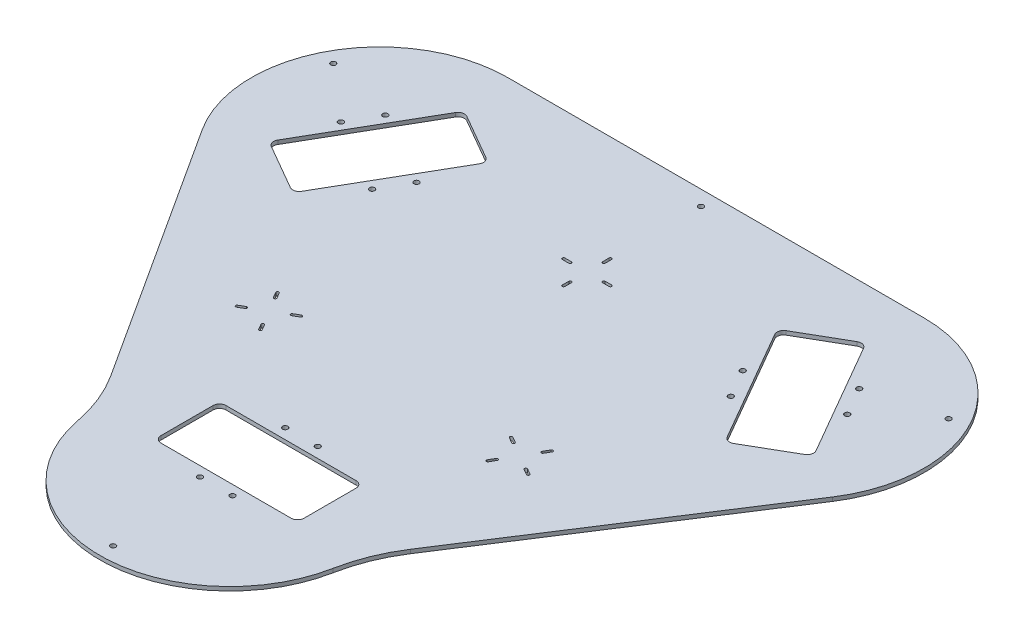
SolidWorks part; units mm, degrees
ref_plane "Front Plane" through (0, 0, 0) normal (0, 0, 1) x (1, 0, 0)
ref_plane "Top Plane" through (0, 0, 0) normal (0, 1, 0) x (1, 0, 0)
ref_plane "Right Plane" through (0, 0, 0) normal (1, 0, 0) x (0, 0, -1)
sketch "Sketch2" plane through (0, 0, 0) normal (0, 1, 0) x (1, 0, 0)
  line L0 (0, 0) -> (0, -160) construction
  line L1 (-113.959, -159.7076) -> (-242.8524, 39.5739)
  line L2 (116.6028, -159.7076) -> (244.0604, 37.3539)
  line L3 (-160.0904, 191.6683) -> (160.0904, 191.6683)
  line L8 (0, 0) -> (138.5641, 80) construction
  line L12 (0, 0) -> (-138.5641, 80) construction
  line L40 (-120, 0) -> (120, 0) construction
  line L57 (138.5641, 80) -> (163.5641, 36.6987)
  line L81 (156.8653, 148.3013) -> (206.8653, 61.6987)
  line L85 (170.3942, 34.8686) -> (187.7147, 44.8686)
  line L86 (138.5641, 80) -> (113.5641, 123.3013)
  line L87 (115.3942, 130.1314) -> (150.0352, 150.1314)
  line L91 (-50, -135) -> (50, -135)
  line L92 (-55, -140) -> (-55, -180)
  line L93 (-50, -185) -> (50, -185)
  line L94 (55, -140) -> (55, -180)
  line L95 (-55, -135) -> (55, -185) construction
  line L96 (-55, -185) -> (55, -135) construction
  line L97 (205.0352, 54.8686) -> (187.7147, 44.8686)
  line L98 (-138.5641, 80) -> (-163.5641, 36.6987)
  line L99 (-170.3942, 34.8686) -> (-205.0352, 54.8686)
  line L100 (-206.8653, 61.6987) -> (-156.8653, 148.3013)
  line L101 (-150.0352, 150.1314) -> (-115.3942, 130.1314)
  line L102 (-113.5641, 123.3013) -> (-138.5641, 80)
  line L103 (-138.5641, 80) -> (-181.8653, 105) construction
  line L104 (-181.8653, 105) -> (-188.3999, 108.7727) construction
  line L105 (-182.1499, 119.598) -> (-194.6499, 97.9474) construction
  line L106 (-138.5641, 80) -> (-131.6359, 76) construction
  line L107 (-137.8859, 65.1747) -> (-125.3859, 86.8253) construction
  line L108 (138.5641, 80) -> (181.8653, 105) construction
  line L109 (181.8653, 105) -> (188.3999, 108.7727) construction
  line L110 (182.1499, 119.598) -> (194.6499, 97.9474) construction
  line L111 (138.5641, 80) -> (131.6359, 76) construction
  line L112 (125.3859, 86.8253) -> (137.8859, 65.1747) construction
  line L113 (0, -135) -> (0, -127) construction
  line L114 (-12.5, -127) -> (12.5, -127) construction
  line L115 (0, -185) -> (0, -192.5455) construction
  line L116 (-12.5, -192.5455) -> (12.5, -192.5455) construction
  arc A0 (244.0604, 37.3539) -> (160.0904, 191.6683) centre (160.0904, 91.665) ccw
  arc A1 (-242.8524, 39.5739) -> (-160.0904, 191.6683) centre (-160.0904, 93.1036) cw
  arc A2 (-96.8788, -202.2176) -> (99.5226, -202.2176) centre (1.3219, -183.3333) ccw
  arc A3 (-113.959, -159.7076) -> (-96.8788, -202.2176) centre (-214.7197, -224.8788) cw
  arc A4 (116.6028, -159.7076) -> (99.5226, -202.2176) centre (217.3635, -224.8788) ccw
  circle A36 centre (-182.1499, 119.598) radius 2
  circle A37 centre (-194.6499, 97.9474) radius 2
  circle A38 centre (-125.3859, 86.8253) radius 2
  circle A39 centre (-137.8859, 65.1747) radius 2
  circle A41 centre (194.6499, 97.9474) radius 2
  circle A42 centre (182.1499, 119.598) radius 2
  circle A43 centre (125.3859, 86.8253) radius 2
  circle A44 centre (137.8859, 65.1747) radius 2
  circle A45 centre (12.5, -127) radius 2
  circle A46 centre (-12.5, -127) radius 2
  circle A47 centre (12.5, -192.5455) radius 2
  circle A48 centre (-12.5, -192.5455) radius 2
  arc A49 (-163.5641, 36.6987) -> (-170.3942, 34.8686) centre (-167.8942, 39.1987) cw
  arc A50 (-205.0352, 54.8686) -> (-206.8653, 61.6987) centre (-202.5352, 59.1987) cw
  arc A51 (-150.0352, 150.1314) -> (-156.8653, 148.3013) centre (-152.5352, 145.8013) ccw
  arc A52 (-113.5641, 123.3013) -> (-115.3942, 130.1314) centre (-117.8942, 125.8013) ccw
  arc A53 (170.3942, 34.8686) -> (163.5641, 36.6987) centre (167.8942, 39.1987) cw
  arc A54 (205.0352, 54.8686) -> (206.8653, 61.6987) centre (202.5352, 59.1987) ccw
  arc A55 (156.8653, 148.3013) -> (150.0352, 150.1314) centre (152.5352, 145.8013) ccw
  arc A56 (113.5641, 123.3013) -> (115.3942, 130.1314) centre (117.8942, 125.8013) cw
  arc A57 (50, -185) -> (55, -180) centre (50, -180) ccw
  arc A58 (55, -140) -> (50, -135) centre (50, -140) ccw
  arc A59 (-50, -185) -> (-55, -180) centre (-50, -180) cw
  arc A60 (-55, -140) -> (-50, -135) centre (-50, -140) cw
  point P22 (0, 0)
  point P27 (1.3219, -283.3333)
  point P28 (109.299, 226.8566)
  point P29 (246.0227, -24.4047)
  point P40 (-188.3999, 108.7727)
  point P46 (-131.6359, 76)
  point P53 (188.3999, 108.7727)
  point P54 (188.3999, 110.681)
  point P61 (131.6359, 76)
  point P67 (0, -127)
  point P75 (0, -192.5455)
  dimension "D1" = 120
  dimension "D3" = 5
  dimension "D2" = 120
extrude "Boss-Extrude1" add sketch "Sketch2" along normal blind 3
sketch "Sketch4" plane through (0, 3, 0) normal (0, 1, 0) x (1, 0, 0)
  line L0 (0, 0) -> (98, 0) construction
  line L1 (113.5, 13) -> (113.5, -13) construction
  line L2 (0, 0) -> (0, 80.5) construction
  line L5 (113.5, 0) -> (100.5, 0) construction
  line L6 (13, 96) -> (18, 96) construction
  line L9 (0, 0) -> (-98, 0) construction
  line L10 (113.5, 0) -> (126.5, 0) construction
  line L13 (113.5, 13) -> (113.5, 18) construction
  line L16 (-113.5, 13) -> (-113.5, -13) construction
  line L18 (-126.5, 0) -> (-100.5, 0) construction
  line L27 (-100.5, 0) -> (-95.5, 0) construction
  line L49 (13, 97) -> (18, 97)
  line L70 (13, 95) -> (18, 95)
  line L73 (-13, 96) -> (-18, 96) construction
  line L74 (-13, 97) -> (-18, 97)
  line L77 (-13, 95) -> (-18, 95)
  line L83 (-100.5, 1) -> (-95.5, 1)
  line L91 (112.5, 13) -> (112.5, 18)
  line L94 (0, 83) -> (0, 78) construction
  line L95 (1, 83) -> (1, 78)
  line L96 (-1, 83) -> (-1, 78)
  line L97 (0, 109) -> (0, 83) construction
  line L98 (0, 109) -> (0, 114) construction
  line L99 (1, 109) -> (1, 114)
  line L100 (-1, 109) -> (-1, 114)
  line L101 (-13, 96) -> (13, 96) construction
  line L104 (114.5, 13) -> (114.5, 18)
  line L107 (113.5, -13) -> (113.5, -18) construction
  line L112 (-100.5, -1) -> (-95.5, -1)
  line L115 (-113.5, 13) -> (-113.5, 18) construction
  line L118 (-112.5, 13) -> (-112.5, 18)
  line L119 (-114.5, 13) -> (-114.5, 18)
  line L120 (-113.5, -13) -> (-113.5, -18) construction
  line L121 (-112.5, -13) -> (-112.5, -18)
  line L122 (-114.5, -13) -> (-114.5, -18)
  line L123 (-126.5, 0) -> (-131.5, 0) construction
  line L124 (-126.5, 1) -> (-131.5, 1)
  line L125 (-126.5, -1) -> (-131.5, -1)
  line L126 (112.5, -13) -> (112.5, -18)
  line L127 (114.5, -13) -> (114.5, -18)
  line L128 (126.5, 0) -> (131.5, 0) construction
  line L129 (126.5, 1) -> (131.5, 1)
  line L130 (126.5, -1) -> (131.5, -1)
  line L131 (100.5, 0) -> (95.5, 0) construction
  line L132 (100.5, 1) -> (95.5, 1)
  line L133 (100.5, -1) -> (95.5, -1)
  arc A70 (13, 97) -> (13, 95) centre (13, 96) ccw
  arc A71 (18, 95) -> (18, 97) centre (18, 96) ccw
  arc A72 (-13, 97) -> (-13, 95) centre (-13, 96) cw
  arc A73 (-18, 95) -> (-18, 97) centre (-18, 96) cw
  arc A74 (1, 109) -> (-1, 109) centre (0, 109) cw
  arc A75 (-1, 114) -> (1, 114) centre (0, 114) cw
  arc A76 (1, 83) -> (-1, 83) centre (0, 83) ccw
  arc A77 (-1, 78) -> (1, 78) centre (0, 78) ccw
  arc A94 (-100.5, 1) -> (-100.5, -1) centre (-100.5, 0) ccw
  arc A95 (-95.5, -1) -> (-95.5, 1) centre (-95.5, 0) ccw
  arc A96 (-112.5, 13) -> (-114.5, 13) centre (-113.5, 13) cw
  arc A97 (-114.5, 18) -> (-112.5, 18) centre (-113.5, 18) cw
  arc A98 (-112.5, -13) -> (-114.5, -13) centre (-113.5, -13) ccw
  arc A99 (-114.5, -18) -> (-112.5, -18) centre (-113.5, -18) ccw
  arc A100 (-126.5, 1) -> (-126.5, -1) centre (-126.5, 0) cw
  arc A101 (-131.5, -1) -> (-131.5, 1) centre (-131.5, 0) cw
  arc A102 (112.5, 13) -> (114.5, 13) centre (113.5, 13) ccw
  arc A103 (114.5, 18) -> (112.5, 18) centre (113.5, 18) ccw
  arc A104 (112.5, -13) -> (114.5, -13) centre (113.5, -13) cw
  arc A105 (114.5, -18) -> (112.5, -18) centre (113.5, -18) cw
  arc A106 (126.5, 1) -> (126.5, -1) centre (126.5, 0) ccw
  arc A107 (131.5, -1) -> (131.5, 1) centre (131.5, 0) ccw
  arc A108 (100.5, 1) -> (100.5, -1) centre (100.5, 0) cw
  arc A109 (95.5, -1) -> (95.5, 1) centre (95.5, 0) cw
  point P4 (0, 0)
  point P9 (0, 80.5)
  point P18 (15.5, 96)
  point P25 (-98, 0)
  point P33 (-15.5, 96)
  point P40 (129, 0)
  point P45 (113.5, 15.5)
  point P54 (113.5, -15.5)
  point P60 (98, 0)
  point P70 (-113.5, 15.5)
  point P77 (-113.5, -15.5)
  point P84 (-129, 0)
  point P97 (0, 111.5)
extrude "Cut-Extrude2" [suppressed] cut sketch "Sketch4" against normal blind 3
sketch "Sketch5" plane through (0, 3, 0) normal (0, 1, 0) x (1, 0, 0)
  line L0 (0, 180.1683) -> (0, 191.6683) construction
  line L1 (0, 180.1683) -> (0, 0) construction
  line L2 (0, 0) -> (0, -271.8333) construction
  line L3 (0, 0) -> (236.508, 133.9665) construction
  line L4 (236.508, 133.9665) -> (247.5831, 140.0972) construction
  line L5 (0, 0) -> (-236.508, 133.9665) construction
  line L6 (-236.508, 133.9665) -> (-247.0087, 139.5816) construction
  circle A0 centre (0, 180.1683) radius 2
  circle A1 centre (236.508, 133.9665) radius 2
  circle A2 centre (-236.508, 133.9665) radius 2
  circle A3 centre (0, -271.8333) radius 2
extrude "Cut-Extrude3" cut sketch "Sketch5" against normal blind 92
sketch "Sketch6" plane through (0, 3, 0) normal (0, 1, 0) x (1, 0, 0)
  line L0 (-55, -140) -> (-55, -180) construction
  line L1 (-50, -135) -> (50, -135) construction
  line L2 (-50, -185) -> (50, -185) construction
  line L3 (-138.5641, 80) -> (0, 0) construction
  line L4 (0, 0) -> (138.5641, 80) construction
  line L5 (0, 0) -> (0, -135) construction
  line L9 (55, -140) -> (55, -180) construction
  line L10 (115.3942, 130.1314) -> (150.0352, 150.1314) construction
  line L11 (156.8653, 148.3013) -> (206.8653, 61.6987) construction
  line L12 (163.5641, 36.6987) -> (113.5641, 123.3013) construction
  line L13 (205.0352, 54.8686) -> (170.3942, 34.8686) construction
  line L14 (-150.0352, 150.1314) -> (-115.3942, 130.1314) construction
  line L15 (-206.8653, 61.6987) -> (-156.8653, 148.3013) construction
  line L16 (-170.3942, 34.8686) -> (-205.0352, 54.8686) construction
  line L17 (-113.5641, 123.3013) -> (-163.5641, 36.6987) construction
  line L18 (-55, -140) -> (-55, -180)
  line L19 (-50, -135) -> (50, -135)
  line L20 (-50, -185) -> (50, -185)
  line L21 (55, -140) -> (55, -180)
  line L22 (115.3942, 130.1314) -> (150.0352, 150.1314)
  line L23 (156.8653, 148.3013) -> (206.8653, 61.6987)
  line L24 (163.5641, 36.6987) -> (113.5641, 123.3013)
  line L25 (205.0352, 54.8686) -> (170.3942, 34.8686)
  line L26 (-150.0352, 150.1314) -> (-115.3942, 130.1314)
  line L27 (-206.8653, 61.6987) -> (-156.8653, 148.3013)
  line L28 (-170.3942, 34.8686) -> (-205.0352, 54.8686)
  line L29 (-113.5641, 123.3013) -> (-163.5641, 36.6987)
  line L32 (1702.5791, -197.4727) -> (1830.0367, -0.4111)
  line L33 (116.6028, -159.7076) -> (244.0604, 37.3539)
  line L34 (160.0904, 191.6683) -> (-160.0904, 191.6683)
  line L35 (1600.8702, 153.9033) -> (1585.9763, 153.9033)
  line L39 (-242.8524, 39.5739) -> (-113.959, -159.7076)
  line L40 (1530.9763, -177.765) -> (1530.9763, -217.765)
  line L41 (1535.9763, -172.765) -> (1635.9763, -172.765)
  line L42 (1535.9763, -222.765) -> (1635.9763, -222.765)
  line L43 (1640.9763, -177.765) -> (1640.9763, -217.765)
  line L44 (1701.3705, 92.3664) -> (1736.0115, 112.3664)
  line L45 (1742.8416, 110.5363) -> (1792.8416, 23.9337)
  line L46 (1749.5404, -1.0663) -> (1699.5404, 85.5363)
  line L47 (1791.0115, 17.1036) -> (1756.3705, -2.8964)
  line L48 (1435.9411, 112.3664) -> (1470.5821, 92.3664)
  line L49 (1379.111, 23.9337) -> (1429.111, 110.5363)
  line L50 (1415.5821, -2.8964) -> (1380.9411, 17.1036)
  line L51 (1472.4122, 85.5363) -> (1422.4122, -1.0663)
  line L52 (1244.7506, 153.9033) -> (1929.8459, 153.9033)
  line L53 (1244.7506, 153.9033) -> (1587.2982, -375.7078)
  line L54 (1766.3079, -98.9419) -> (1587.2982, -375.7078) construction
  line L55 (1791.0115, -60.7478) -> (1929.8459, 153.9033) construction
  line L56 (1585.9763, 153.9033) -> (1600.8702, 153.9033)
  line L57 (1929.8459, 153.9033) -> (1587.2982, -375.7078)
  line L58 (1585.9763, 153.9033) -> (1587.2982, -375.7078) construction
  line L59 (116.6028, -159.7076) -> (244.0604, 37.3539)
  line L60 (160.0904, 191.6683) -> (-160.0904, 191.6683)
  line L61 (-242.8524, 39.5739) -> (-113.959, -159.7076)
  line L62 (1244.7506, 153.9033) -> (1758.5721, -110.9022) construction
  line L63 (1929.8459, 153.9033) -> (1416.0244, -110.9022) construction
  line L64 (1929.8459, 153.9033) -> (1746.0667, 53.9) construction
  line L65 (1746.0667, 53.9) -> (1423.1001, -121.842) construction
  line L66 (1244.7506, 153.9033) -> (1425.886, 55.3386) construction
  line L67 (1425.886, 55.3386) -> (1756.0428, -114.8126) construction
  line L68 (23.7375, -963.5223) -> (23.7375, -1123.5223) construction
  line L69 (-90.2215, -1123.23) -> (-219.115, -923.9485)
  line L70 (140.3403, -1123.23) -> (267.7979, -926.1684)
  line L71 (-136.3529, -771.854) -> (183.8278, -771.854)
  line L72 (23.7375, -963.5223) -> (162.3015, -883.5223) construction
  line L73 (23.7375, -963.5223) -> (-114.8266, -883.5223) construction
  line L74 (-96.2625, -963.5223) -> (143.7375, -963.5223) construction
  line L75 (162.3015, -883.5223) -> (187.3015, -926.8236)
  line L76 (180.6028, -815.2211) -> (230.6028, -901.8236)
  line L77 (194.1316, -928.6537) -> (211.4522, -918.6537)
  line L78 (162.3015, -883.5223) -> (137.3015, -840.2211)
  line L79 (139.1316, -833.3909) -> (173.7727, -813.3909)
  line L80 (-26.2625, -1098.5223) -> (73.7375, -1098.5223)
  line L81 (-31.2625, -1103.5223) -> (-31.2625, -1143.5223)
  line L82 (-26.2625, -1148.5223) -> (73.7375, -1148.5223)
  line L83 (78.7375, -1103.5223) -> (78.7375, -1143.5223)
  line L84 (-31.2625, -1098.5223) -> (78.7375, -1148.5223) construction
  line L85 (-31.2625, -1148.5223) -> (78.7375, -1098.5223) construction
  line L86 (228.7727, -908.6537) -> (211.4522, -918.6537)
  line L87 (-114.8266, -883.5223) -> (-139.8266, -926.8236)
  line L88 (-146.6567, -928.6537) -> (-181.2978, -908.6537)
  line L89 (-183.1279, -901.8236) -> (-133.1279, -815.2211)
  line L90 (-126.2978, -813.3909) -> (-91.6567, -833.3909)
  line L91 (-89.8266, -840.2211) -> (-114.8266, -883.5223)
  line L92 (-114.8266, -883.5223) -> (-158.1279, -858.5223) construction
  line L93 (-158.1279, -858.5223) -> (-164.6624, -854.7496) construction
  line L94 (-158.4124, -843.9243) -> (-170.9124, -865.5749) construction
  line L95 (-114.8266, -883.5223) -> (-107.8984, -887.5223) construction
  line L96 (-114.1484, -898.3477) -> (-101.6484, -876.697) construction
  line L97 (162.3015, -883.5223) -> (205.6028, -858.5223) construction
  line L98 (205.6028, -858.5223) -> (212.1373, -854.7496) construction
  line L99 (205.8873, -843.9243) -> (218.3873, -865.5749) construction
  line L100 (162.3015, -883.5223) -> (155.3733, -887.5223) construction
  line L101 (149.1233, -876.697) -> (161.6233, -898.3477) construction
  line L102 (23.7375, -1098.5223) -> (23.7375, -1090.5223) construction
  line L103 (11.2375, -1090.5223) -> (36.2375, -1090.5223) construction
  line L104 (23.7375, -1148.5223) -> (23.7375, -1156.0678) construction
  line L105 (11.2375, -1156.0678) -> (36.2375, -1156.0678) construction
  line L106 (-132.7147, 140.1314) -> (132.7147, 140.1314) construction
  line L107 (-50, 28.8675) -> (230.3476, -132.9913) construction
  line L108 (25.0594, 14.468) -> (-158.1859, -91.3287) construction
  line L109 (138.5641, 80) -> (0, -135) construction
  line L110 (0, -135) -> (-138.5641, 80) construction
  line L111 (0, 0) -> (0, 140.1314) construction
  line L112 (13, 140.1314) -> (18, 140.1314) construction
  line L113 (13, 141.1314) -> (18, 141.1314)
  line L114 (13, 139.1314) -> (18, 139.1314)
  line L115 (-13, 140.1314) -> (-18, 140.1314) construction
  line L116 (-13, 141.1314) -> (-18, 141.1314)
  line L117 (-13, 139.1314) -> (-18, 139.1314)
  line L118 (0, 127.1314) -> (0, 122.1314) construction
  line L119 (1, 127.1314) -> (1, 122.1314)
  line L120 (-1, 127.1314) -> (-1, 122.1314)
  line L121 (0, 153.1314) -> (0, 127.1314) construction
  line L122 (0, 153.1314) -> (0, 158.1314) construction
  line L123 (1, 153.1314) -> (1, 158.1314)
  line L124 (-1, 153.1314) -> (-1, 158.1314)
  line L125 (-13, 140.1314) -> (13, 140.1314) construction
  line L126 (110.0978, -63.565) -> (105.7677, -61.065) construction
  line L128 (109.5978, -64.431) -> (105.2677, -61.931)
  line L129 (110.5978, -62.699) -> (106.2677, -60.199)
  line L130 (132.6145, -76.565) -> (136.9446, -79.065) construction
  line L131 (132.1145, -77.431) -> (136.4446, -79.931)
  line L132 (133.1145, -75.699) -> (137.4446, -78.199)
  line L133 (127.8561, -58.8067) -> (130.3561, -54.4765) construction
  line L134 (126.9901, -58.3067) -> (129.4901, -53.9765)
  line L135 (128.7222, -59.3067) -> (131.2222, -54.9765)
  line L136 (114.8561, -81.3233) -> (127.8561, -58.8067) construction
  line L137 (114.8561, -81.3233) -> (112.3561, -85.6535) construction
  line L138 (113.9901, -80.8233) -> (111.4901, -85.1535)
  line L139 (115.7222, -81.8233) -> (113.2222, -86.1535)
  line L140 (132.6145, -76.565) -> (110.0978, -63.565) construction
  line L141 (0, 0) -> (-160.0904, -92.4401) construction
  line L142 (-127.8561, -58.8067) -> (-130.3561, -54.4765) construction
  line L143 (-128.7222, -59.3067) -> (-131.2222, -54.9765)
  line L144 (-126.9901, -58.3067) -> (-129.4901, -53.9765)
  line L145 (-114.8561, -81.3233) -> (-112.3561, -85.6535) construction
  line L146 (-115.7222, -81.8233) -> (-113.2222, -86.1535)
  line L147 (-113.9901, -80.8233) -> (-111.4901, -85.1535)
  line L148 (-110.0978, -63.565) -> (-105.7677, -61.065) construction
  line L149 (-110.5978, -62.699) -> (-106.2677, -60.199)
  line L150 (-109.5978, -64.431) -> (-105.2677, -61.931)
  line L151 (-132.6145, -76.565) -> (-110.0978, -63.565) construction
  line L152 (-132.6145, -76.565) -> (-136.9446, -79.065) construction
  line L153 (-133.1145, -75.699) -> (-137.4446, -78.199)
  line L154 (-132.1145, -77.431) -> (-136.4446, -79.931)
  line L155 (-114.8561, -81.3233) -> (-127.8561, -58.8067) construction
  line L156 (-1279.2979, -369.2933) -> (-1281.7979, -364.9632) construction
  line L157 (-1280.1639, -369.7933) -> (-1282.6639, -365.4632)
  line L158 (-1278.4318, -368.7933) -> (-1280.9318, -364.4632)
  line L159 (-1266.2979, -391.81) -> (-1263.7979, -396.1401) construction
  line L160 (-1267.1639, -392.31) -> (-1264.6639, -396.6401)
  line L161 (-1265.4318, -391.31) -> (-1262.9318, -395.6401)
  line L162 (-1261.5395, -374.0516) -> (-1257.2094, -371.5516) construction
  line L163 (-1262.0395, -373.1856) -> (-1257.7094, -370.6856)
  line L164 (-1261.0395, -374.9177) -> (-1256.7094, -372.4177)
  line L165 (-1284.0562, -387.0516) -> (-1261.5395, -374.0516) construction
  line L166 (-1284.0562, -387.0516) -> (-1288.3863, -389.5516) construction
  line L167 (-1284.5562, -386.1856) -> (-1288.8863, -388.6856)
  line L168 (-1283.5562, -387.9177) -> (-1287.8863, -390.4177)
  line L169 (-1266.2979, -391.81) -> (-1279.2979, -369.2933) construction
  line L170 (121.3561, -70.065) -> (124.2581, -65.0387) construction
  arc A0 (-55, -180) -> (-50, -185) centre (-50, -180) ccw construction
  arc A1 (-50, -135) -> (-55, -140) centre (-50, -140) ccw construction
  arc A2 (55, -140) -> (50, -135) centre (50, -140) ccw construction
  arc A3 (50, -185) -> (55, -180) centre (50, -180) ccw construction
  arc A4 (115.3942, 130.1314) -> (113.5641, 123.3013) centre (117.8942, 125.8013) ccw construction
  arc A5 (267.7979, -926.1684) -> (183.8278, -771.854) centre (183.8278, -871.8573) ccw
  arc A6 (-219.115, -923.9485) -> (-136.3529, -771.854) centre (-136.3529, -870.4187) cw
  arc A7 (-73.1414, -1165.74) -> (123.2601, -1165.74) centre (25.0594, -1146.8557) ccw
  arc A8 (-90.2215, -1123.23) -> (-73.1414, -1165.74) centre (-190.9822, -1188.4011) cw
  arc A9 (140.3403, -1123.23) -> (123.2601, -1165.74) centre (241.101, -1188.4011) ccw
  arc A15 (156.8653, 148.3013) -> (150.0352, 150.1314) centre (152.5352, 145.8013) ccw construction
  arc A16 (163.5641, 36.6987) -> (170.3942, 34.8686) centre (167.8942, 39.1987) ccw construction
  arc A17 (205.0352, 54.8686) -> (206.8653, 61.6987) centre (202.5352, 59.1987) ccw construction
  arc A18 (-206.8653, 61.6987) -> (-205.0352, 54.8686) centre (-202.5352, 59.1987) ccw construction
  arc A19 (-170.3942, 34.8686) -> (-163.5641, 36.6987) centre (-167.8942, 39.1987) ccw construction
  arc A20 (-113.5641, 123.3013) -> (-115.3942, 130.1314) centre (-117.8942, 125.8013) ccw construction
  arc A21 (-150.0352, 150.1314) -> (-156.8653, 148.3013) centre (-152.5352, 145.8013) ccw construction
  arc A22 (-55, -180) -> (-50, -185) centre (-50, -180) ccw
  arc A23 (-50, -135) -> (-55, -140) centre (-50, -140) ccw
  arc A24 (55, -140) -> (50, -135) centre (50, -140) ccw
  arc A25 (50, -185) -> (55, -180) centre (50, -180) ccw
  arc A26 (115.3942, 130.1314) -> (113.5641, 123.3013) centre (117.8942, 125.8013) ccw
  arc A27 (156.8653, 148.3013) -> (150.0352, 150.1314) centre (152.5352, 145.8013) ccw
  arc A28 (163.5641, 36.6987) -> (170.3942, 34.8686) centre (167.8942, 39.1987) ccw
  arc A29 (205.0352, 54.8686) -> (206.8653, 61.6987) centre (202.5352, 59.1987) ccw
  arc A30 (-206.8653, 61.6987) -> (-205.0352, 54.8686) centre (-202.5352, 59.1987) ccw
  arc A31 (-170.3942, 34.8686) -> (-163.5641, 36.6987) centre (-167.8942, 39.1987) ccw
  arc A32 (-113.5641, 123.3013) -> (-115.3942, 130.1314) centre (-117.8942, 125.8013) ccw
  arc A33 (-150.0352, 150.1314) -> (-156.8653, 148.3013) centre (-152.5352, 145.8013) ccw
  arc A34 (1702.5791, -197.4727) -> (1685.499, -239.9826) centre (1803.3398, -262.6438) ccw
  arc A35 (1830.0367, -0.4111) -> (1746.0667, 153.9033) centre (1746.0667, 53.9) ccw
  arc A36 (1425.886, 153.9033) -> (1343.1239, 1.8089) centre (1425.886, 55.3386) ccw
  arc A37 (1489.0975, -239.9826) -> (1685.499, -239.9826) centre (1587.2982, -221.0983) ccw
  arc A38 (1530.9763, -217.765) -> (1535.9763, -222.765) centre (1535.9763, -217.765) ccw
  arc A39 (1535.9763, -172.765) -> (1530.9763, -177.765) centre (1535.9763, -177.765) ccw
  arc A40 (1640.9763, -177.765) -> (1635.9763, -172.765) centre (1635.9763, -177.765) ccw
  arc A41 (1635.9763, -222.765) -> (1640.9763, -217.765) centre (1635.9763, -217.765) ccw
  arc A42 (1701.3705, 92.3664) -> (1699.5404, 85.5363) centre (1703.8705, 88.0363) ccw
  arc A43 (1742.8416, 110.5363) -> (1736.0115, 112.3664) centre (1738.5115, 108.0363) ccw
  arc A44 (1749.5404, -1.0663) -> (1756.3705, -2.8964) centre (1753.8705, 1.4337) ccw
  arc A45 (1791.0115, 17.1036) -> (1792.8416, 23.9337) centre (1788.5115, 21.4337) ccw
  arc A46 (1379.111, 23.9337) -> (1380.9411, 17.1036) centre (1383.4411, 21.4337) ccw
  arc A47 (1415.5821, -2.8964) -> (1422.4122, -1.0663) centre (1418.0821, 1.4337) ccw
  arc A48 (1472.4122, 85.5363) -> (1470.5821, 92.3664) centre (1468.0821, 88.0363) ccw
  arc A49 (1435.9411, 112.3664) -> (1429.111, 110.5363) centre (1433.4411, 108.0363) ccw
  arc A50 (116.6028, -159.7076) -> (99.5226, -202.2176) centre (217.3635, -224.8788) ccw
  arc A51 (244.0604, 37.3539) -> (160.0904, 191.6683) centre (160.0904, 91.665) ccw
  arc A52 (-160.0904, 191.6683) -> (-242.8524, 39.5739) centre (-160.0904, 93.1036) ccw
  arc A53 (-96.8788, -202.2176) -> (-113.959, -159.7076) centre (-214.7197, -224.8788) ccw
  arc A54 (-96.8788, -202.2176) -> (99.5226, -202.2176) centre (1.3219, -183.3333) ccw
  arc A55 (116.6028, -159.7076) -> (99.5226, -202.2176) centre (217.3635, -224.8788) ccw
  arc A56 (244.0604, 37.3539) -> (160.0904, 191.6683) centre (160.0904, 91.665) ccw
  arc A57 (-160.0904, 191.6683) -> (-242.8524, 39.5739) centre (-160.0904, 93.1036) ccw
  arc A58 (-96.8788, -202.2176) -> (-113.959, -159.7076) centre (-214.7197, -224.8788) ccw
  arc A59 (-96.8788, -202.2176) -> (99.5226, -202.2176) centre (1.3219, -183.3333) ccw
  circle A60 centre (-158.4124, -843.9243) radius 2
  circle A61 centre (-170.9124, -865.5749) radius 2
  circle A62 centre (-101.6484, -876.697) radius 2
  circle A63 centre (-114.1484, -898.3477) radius 2
  circle A64 centre (218.3873, -865.5749) radius 2
  circle A65 centre (205.8873, -843.9243) radius 2
  circle A66 centre (149.1233, -876.697) radius 2
  circle A67 centre (161.6233, -898.3477) radius 2
  circle A68 centre (36.2375, -1090.5223) radius 2
  circle A69 centre (11.2375, -1090.5223) radius 2
  circle A70 centre (36.2375, -1156.0678) radius 2
  circle A71 centre (11.2375, -1156.0678) radius 2
  arc A72 (-139.8266, -926.8236) -> (-146.6567, -928.6537) centre (-144.1567, -924.3236) cw
  arc A73 (-181.2978, -908.6537) -> (-183.1279, -901.8236) centre (-178.7978, -904.3236) cw
  arc A74 (-126.2978, -813.3909) -> (-133.1279, -815.2211) centre (-128.7978, -817.7211) ccw
  arc A75 (-89.8266, -840.2211) -> (-91.6567, -833.3909) centre (-94.1567, -837.7211) ccw
  arc A76 (194.1316, -928.6537) -> (187.3015, -926.8236) centre (191.6316, -924.3236) cw
  arc A77 (228.7727, -908.6537) -> (230.6028, -901.8236) centre (226.2727, -904.3236) ccw
  arc A78 (180.6028, -815.2211) -> (173.7727, -813.3909) centre (176.2727, -817.7211) ccw
  arc A79 (137.3015, -840.2211) -> (139.1316, -833.3909) centre (141.6316, -837.7211) cw
  arc A80 (73.7375, -1148.5223) -> (78.7375, -1143.5223) centre (73.7375, -1143.5223) ccw
  arc A81 (78.7375, -1103.5223) -> (73.7375, -1098.5223) centre (73.7375, -1103.5223) ccw
  arc A82 (-26.2625, -1148.5223) -> (-31.2625, -1143.5223) centre (-26.2625, -1143.5223) cw
  arc A83 (-31.2625, -1103.5223) -> (-26.2625, -1098.5223) centre (-26.2625, -1103.5223) cw
  arc A84 (13, 141.1314) -> (13, 139.1314) centre (13, 140.1314) ccw
  arc A85 (18, 139.1314) -> (18, 141.1314) centre (18, 140.1314) ccw
  arc A86 (-13, 141.1314) -> (-13, 139.1314) centre (-13, 140.1314) cw
  arc A87 (-18, 139.1314) -> (-18, 141.1314) centre (-18, 140.1314) cw
  arc A88 (1, 153.1314) -> (-1, 153.1314) centre (0, 153.1314) cw
  arc A89 (-1, 158.1314) -> (1, 158.1314) centre (0, 158.1314) cw
  arc A90 (1, 127.1314) -> (-1, 127.1314) centre (0, 127.1314) ccw
  arc A91 (-1, 122.1314) -> (1, 122.1314) centre (0, 122.1314) ccw
  arc A92 (109.5978, -64.431) -> (110.5978, -62.699) centre (110.0978, -63.565) ccw
  arc A93 (106.2677, -60.199) -> (105.2677, -61.931) centre (105.7677, -61.065) ccw
  arc A94 (132.1145, -77.431) -> (133.1145, -75.699) centre (132.6145, -76.565) cw
  arc A95 (137.4446, -78.199) -> (136.4446, -79.931) centre (136.9446, -79.065) cw
  arc A96 (113.9901, -80.8233) -> (115.7222, -81.8233) centre (114.8561, -81.3233) cw
  arc A97 (113.2222, -86.1535) -> (111.4901, -85.1535) centre (112.3561, -85.6535) cw
  arc A98 (126.9901, -58.3067) -> (128.7222, -59.3067) centre (127.8561, -58.8067) ccw
  arc A99 (131.2222, -54.9765) -> (129.4901, -53.9765) centre (130.3561, -54.4765) ccw
  arc A100 (-128.7222, -59.3067) -> (-126.9901, -58.3067) centre (-127.8561, -58.8067) ccw
  arc A101 (-129.4901, -53.9765) -> (-131.2222, -54.9765) centre (-130.3561, -54.4765) ccw
  arc A102 (-115.7222, -81.8233) -> (-113.9901, -80.8233) centre (-114.8561, -81.3233) cw
  arc A103 (-111.4901, -85.1535) -> (-113.2222, -86.1535) centre (-112.3561, -85.6535) cw
  arc A104 (-133.1145, -75.699) -> (-132.1145, -77.431) centre (-132.6145, -76.565) cw
  arc A105 (-136.4446, -79.931) -> (-137.4446, -78.199) centre (-136.9446, -79.065) cw
  arc A106 (-110.5978, -62.699) -> (-109.5978, -64.431) centre (-110.0978, -63.565) ccw
  arc A107 (-105.2677, -61.931) -> (-106.2677, -60.199) centre (-105.7677, -61.065) ccw
  arc A108 (-1280.1639, -369.7933) -> (-1278.4318, -368.7933) centre (-1279.2979, -369.2933) ccw
  arc A109 (-1280.9318, -364.4632) -> (-1282.6639, -365.4632) centre (-1281.7979, -364.9632) ccw
  arc A110 (-1267.1639, -392.31) -> (-1265.4318, -391.31) centre (-1266.2979, -391.81) cw
  arc A111 (-1262.9318, -395.6401) -> (-1264.6639, -396.6401) centre (-1263.7979, -396.1401) cw
  arc A112 (-1284.5562, -386.1856) -> (-1283.5562, -387.9177) centre (-1284.0562, -387.0516) cw
  arc A113 (-1287.8863, -390.4177) -> (-1288.8863, -388.6856) centre (-1288.3863, -389.5516) cw
  arc A114 (-1262.0395, -373.1856) -> (-1261.0395, -374.9177) centre (-1261.5395, -374.0516) ccw
  arc A115 (-1256.7094, -372.4177) -> (-1257.7094, -370.6856) centre (-1257.2094, -371.5516) ccw
  point P135 (23.7375, -963.5223)
  point P140 (25.0594, -1246.8557)
  point P151 (-164.6624, -854.7496)
  point P157 (-107.8984, -887.5223)
  point P164 (212.1373, -854.7496)
  point P165 (212.1373, -852.8414)
  point P172 (155.3733, -887.5223)
  point P178 (23.7375, -1090.5223)
  point P185 (23.7375, -1156.0678)
  point P220 (0, 140.1314)
  point P221 (-121.3561, -70.065)
  point P223 (121.3561, -70.065)
  point P225 (0, 124.6314)
  point P231 (15.5, 140.1314)
  point P243 (-15.5, 140.1314)
  point P252 (0, 155.6314)
  point P258 (129.1061, -56.6416)
  point P264 (107.9327, -62.315)
  point P275 (134.7795, -77.815)
  point P284 (113.6061, -83.4884)
  point P291 (-107.9327, -62.315)
  point P294 (0, 152.1314)
  point P295 (0, 128.1314)
  point P299 (-129.1061, -56.6416)
  point P310 (-113.6061, -83.4884)
  point P319 (-134.7795, -77.815)
  point P325 (-1259.3745, -372.8016)
  point P331 (-1280.5479, -367.1283)
  point P342 (-1265.0479, -393.975)
  point P351 (-1286.2212, -388.3016)
  dimension "D10" = 5
  dimension "D2" = 90
  dimension "D3" = 140.1314
  dimension "D4" = 24
  dimension "D5" = 125.47
  dimension "D6" = 117.122
  dimension "D7" = 124.182
  dimension "D8" = 120
  dimension "D9" = 120
  dimension "D11" = 140.13
  dimension "D12" = 140.13
  dimension "D13" = 90
  dimension "D14" = 90
  dimension "D1" = 0
extrude "Cut-Extrude4" [suppressed] cut sketch "Sketch6" against normal blind 10 contours L154 A105 L153 A104 | A103 L146 A102 L147 | L150 A107 L149 A106 | A100 L144 A101 L143 | L131 A95 L132 A94 | L135 A99 L134 A98 | L128 A93 L129 A92 | L139 A97 L138 A96 | L124 A89 L123 A88 | L117 A87 L116 A86 | L120 A91 L119 A90 | L114 A85 L113 A84
sketch "Sketch7" plane through (0, 3, 0) normal (0, 1, 0) x (1, 0, 0)
  line L1 (123.5, 0.0713) -> (123.5, 0.0004)
  line L7 (-1, 106.0023) -> (1, 106.0023)
  line L12 (123.5, 0.0713) -> (123.5, 0.0004)
  line L17 (140.0054, 0.0713) -> (140, 0.0713)
  line L18 (0, 201.2179) -> (0, 106.0023) construction
  line L19 (0, 191.9366) -> (0, 106.0023) construction
  line L20 (-138.5641, 80) -> (0.0027, -0.0016) construction
  line L21 (116.6028, -159.7076) -> (244.0604, 37.3539)
  line L22 (-55, -140) -> (-55, -180)
  line L23 (50, -135) -> (-50, -135)
  line L24 (55, -180) -> (55, -140)
  line L25 (-50, -185) -> (50, -185)
  line L26 (-55, -140) -> (-55, -180)
  line L27 (50, -135) -> (-50, -135)
  line L28 (55, -180) -> (55, -140)
  line L29 (-50, -185) -> (50, -185)
  line L30 (-163.5641, 36.6987) -> (-113.5641, 123.3013)
  line L31 (-205.0352, 54.8686) -> (-170.3942, 34.8686)
  line L32 (-156.8653, 148.3013) -> (-206.8653, 61.6987)
  line L33 (-115.3942, 130.1314) -> (-150.0352, 150.1314)
  line L34 (-163.5641, 36.6987) -> (-113.5641, 123.3013)
  line L35 (-205.0352, 54.8686) -> (-170.3942, 34.8686)
  line L36 (-156.8653, 148.3013) -> (-206.8653, 61.6987)
  line L37 (-115.3942, 130.1314) -> (-150.0352, 150.1314)
  line L38 (113.5641, 123.3013) -> (163.5641, 36.6987)
  line L39 (150.0352, 150.1314) -> (115.3942, 130.1314)
  line L40 (206.8653, 61.6987) -> (156.8653, 148.3013)
  line L41 (170.3942, 34.8686) -> (205.0352, 54.8686)
  line L42 (113.5641, 123.3013) -> (163.5641, 36.6987)
  line L43 (150.0352, 150.1314) -> (115.3942, 130.1314)
  line L44 (206.8653, 61.6987) -> (156.8653, 148.3013)
  line L45 (170.3942, 34.8686) -> (205.0352, 54.8686)
  line L46 (160.0904, 191.6683) -> (-160.0904, 191.6683)
  line L47 (-242.8524, 39.5739) -> (-113.959, -159.7076)
  line L48 (116.6028, -159.7076) -> (244.0604, 37.3539)
  line L49 (160.0904, 191.6683) -> (-160.0904, 191.6683)
  line L50 (-242.8524, 39.5739) -> (-113.959, -159.7076)
  line L51 (-0.002, 0.0012) -> (0.0027, -0.0016) construction
  line L52 (138.5641, 80) -> (0, 0.0023) construction
  line L53 (0, 0.0023) -> (-0.002, 0.0012) construction
  line L54 (-59.8557, -383.4524) -> (-62.3557, -379.1222) construction
  line L55 (-60.7217, -383.9524) -> (-63.2217, -379.6222)
  line L56 (-58.9896, -382.9524) -> (-61.4896, -378.6222)
  line L57 (-46.8557, -405.969) -> (-44.3557, -410.2991) construction
  line L58 (-47.7217, -406.469) -> (-45.2217, -410.7991)
  line L59 (-45.9896, -405.469) -> (-43.4896, -409.7991)
  line L60 (-42.0973, -388.2107) -> (-37.7672, -385.7107) construction
  line L61 (-42.5973, -387.3447) -> (-38.2672, -384.8447)
  line L62 (-41.5973, -389.0767) -> (-37.2672, -386.5767)
  line L63 (-64.614, -401.2107) -> (-42.0973, -388.2107) construction
  line L64 (-64.614, -401.2107) -> (-68.9441, -403.7107) construction
  line L65 (-65.114, -400.3447) -> (-69.4441, -402.8447)
  line L66 (-64.114, -402.0767) -> (-68.4441, -404.5767)
  line L67 (-46.8557, -405.969) -> (-59.8557, -383.4524) construction
  line L68 (0, 92.5023) -> (0, 0.0023) construction
  line L71 (0.0027, -0.0016) -> (-96.3682, -55.6343) construction
  line L74 (96.3811, -55.6456) -> (0.0027, -0.0016) construction
  line L81 (0, 61.6681) -> (0, 87.6681) construction
  line L82 (-63.1485, -36.4554) -> (-69.2107, -39.9553) construction
  line L85 (-63.148, -36.4563) -> (-69.2104, -39.9559)
  line L88 (-96.9238, -55.955) -> (-158.0619, -91.2521) construction
  line L91 (-69.2108, -39.9552) -> (-68.3448, -39.4552) construction
  line L92 (-79.6031, -45.9552) -> (-96.0577, -55.455) construction
  line L95 (-69.2108, -39.9552) -> (-89.9954, -51.9552) construction
  line L96 (0, 93.6681) -> (0, 0.0023) construction
  line L99 (0, 93.6681) -> (0, -135) construction
  line L102 (0, 87.6681) -> (0, 61.6681) construction
  line L105 (-90.8615, -52.4552) -> (-79.6031, -45.9552) construction
  line L106 (0, 105.5023) -> (0, 110.5023) construction
  line L109 (-1, 105.5023) -> (-1, 110.5023)
  line L110 (-9.9984, 94.6681) -> (10.0016, 94.6681) construction
  line L111 (153.869, -88.8363) -> (266.5057, -153.8671) construction
  line L112 (0, 195.6584) -> (0, 281.696) construction
  line L113 (107.6394, -62.1456) -> (111.9695, -64.6456) construction
  line L114 (0.0027, -0.0016) -> (0, -0.0031)
  line L115 (0.0027, -0.0016) -> (-0.002, 0.0012)
  line L116 (89.1964, -51.4976) -> (119.9034, -69.2262) construction
  line L117 (113.7016, -65.6456) -> (160.1109, -92.4401) construction
  line L118 (-96.3682, -55.6343) -> (-112.8228, -65.1341) construction
  line L121 (-85.9759, -49.6343) -> (-106.7605, -61.6343) construction
  line L124 (-102.8682, -44.3759) -> (-105.3682, -40.0458) construction
  line L127 (-103.7342, -44.8759) -> (-106.2342, -40.5458)
  line L128 (-102.0022, -43.8759) -> (-104.5022, -39.5458)
  line L131 (66.6798, -38.4976) -> (89.1964, -51.4976) construction
  line L132 (-89.8682, -66.8926) -> (-87.3682, -71.2227) construction
  line L133 (108.1394, -61.2796) -> (112.4695, -63.7796)
  line L134 (107.1394, -63.0117) -> (111.4695, -65.5117)
  line L135 (85.1227, -49.1456) -> (80.7926, -46.6456) construction
  line L136 (85.6227, -48.2796) -> (81.2926, -45.7796)
  line L137 (84.6227, -50.0117) -> (80.2926, -47.5117)
  line L138 (89.8811, -66.904) -> (87.3811, -71.2341) construction
  line L139 (90.7471, -67.404) -> (88.2471, -71.7341)
  line L140 (89.015, -66.404) -> (86.515, -70.7341)
  line L141 (102.8811, -44.3873) -> (89.8811, -66.904) construction
  line L142 (102.8811, -44.3873) -> (105.3811, -40.0572) construction
  line L143 (103.7471, -44.8873) -> (106.2471, -40.5572)
  line L144 (102.015, -43.8873) -> (104.515, -39.5572)
  line L145 (85.1227, -49.1456) -> (107.6394, -62.1456) construction
  line L146 (96.3811, -55.6456) -> (79.9266, -46.1456)
  line L147 (-90.7342, -67.3926) -> (-88.2342, -71.7227)
  line L148 (-89.0022, -66.3926) -> (-86.5022, -70.7227)
  line L149 (-85.1099, -49.1343) -> (-80.7798, -46.6343) construction
  line L150 (-85.6099, -48.2682) -> (-81.2798, -45.7682)
  line L151 (-84.6099, -50.0003) -> (-80.2798, -47.5003)
  line L152 (-107.6265, -62.1343) -> (-111.9567, -64.6343) construction
  line L153 (-108.1265, -61.2682) -> (-112.4567, -63.7682)
  line L154 (-107.1265, -63.0003) -> (-111.4567, -65.5003)
  line L155 (-89.8682, -66.8926) -> (-102.8682, -44.3759) construction
  line L156 (1, 105.5023) -> (1, 110.5023)
  line L157 (0, 79.5023) -> (0, 74.5023) construction
  line L158 (-1, 79.5023) -> (-1, 74.5023)
  line L159 (1, 79.5023) -> (1, 74.5023)
  line L160 (13, 92.5023) -> (18, 92.5023) construction
  line L161 (13, 93.5023) -> (18, 93.5023)
  line L162 (13, 91.5023) -> (18, 91.5023)
  line L163 (-13, 92.5023) -> (13, 92.5023) construction
  line L164 (-13, 92.5023) -> (-18, 92.5023) construction
  line L165 (-13, 93.5023) -> (-18, 93.5023)
  line L166 (-13, 91.5023) -> (-18, 91.5023)
  line L167 (0, 79.5023) -> (0, 105.5023) construction
  arc A11 (-60.7217, -383.9524) -> (-58.9896, -382.9524) centre (-59.8557, -383.4524) ccw
  arc A12 (-61.4896, -378.6222) -> (-63.2217, -379.6222) centre (-62.3557, -379.1222) ccw
  arc A13 (-47.7217, -406.469) -> (-45.9896, -405.469) centre (-46.8557, -405.969) cw
  arc A14 (-43.4896, -409.7991) -> (-45.2217, -410.7991) centre (-44.3557, -410.2991) cw
  arc A15 (-50, -135) -> (-55, -140) centre (-50, -140) ccw
  arc A16 (55, -140) -> (50, -135) centre (50, -140) ccw
  arc A17 (50, -185) -> (55, -180) centre (50, -180) ccw
  arc A18 (-55, -180) -> (-50, -185) centre (-50, -180) ccw
  arc A19 (-50, -135) -> (-55, -140) centre (-50, -140) ccw
  arc A20 (55, -140) -> (50, -135) centre (50, -140) ccw
  arc A21 (50, -185) -> (55, -180) centre (50, -180) ccw
  arc A22 (-55, -180) -> (-50, -185) centre (-50, -180) ccw
  arc A23 (-113.5641, 123.3013) -> (-115.3942, 130.1314) centre (-117.8942, 125.8013) ccw
  arc A24 (-170.3942, 34.8686) -> (-163.5641, 36.6987) centre (-167.8942, 39.1987) ccw
  arc A25 (-206.8653, 61.6987) -> (-205.0352, 54.8686) centre (-202.5352, 59.1987) ccw
  arc A26 (-150.0352, 150.1314) -> (-156.8653, 148.3013) centre (-152.5352, 145.8013) ccw
  arc A27 (-113.5641, 123.3013) -> (-115.3942, 130.1314) centre (-117.8942, 125.8013) ccw
  arc A28 (-170.3942, 34.8686) -> (-163.5641, 36.6987) centre (-167.8942, 39.1987) ccw
  arc A29 (-206.8653, 61.6987) -> (-205.0352, 54.8686) centre (-202.5352, 59.1987) ccw
  arc A30 (-150.0352, 150.1314) -> (-156.8653, 148.3013) centre (-152.5352, 145.8013) ccw
  arc A31 (115.3942, 130.1314) -> (113.5641, 123.3013) centre (117.8942, 125.8013) ccw
  arc A32 (156.8653, 148.3013) -> (150.0352, 150.1314) centre (152.5352, 145.8013) ccw
  arc A33 (205.0352, 54.8686) -> (206.8653, 61.6987) centre (202.5352, 59.1987) ccw
  arc A34 (163.5641, 36.6987) -> (170.3942, 34.8686) centre (167.8942, 39.1987) ccw
  arc A35 (115.3942, 130.1314) -> (113.5641, 123.3013) centre (117.8942, 125.8013) ccw
  arc A36 (156.8653, 148.3013) -> (150.0352, 150.1314) centre (152.5352, 145.8013) ccw
  arc A37 (205.0352, 54.8686) -> (206.8653, 61.6987) centre (202.5352, 59.1987) ccw
  arc A38 (163.5641, 36.6987) -> (170.3942, 34.8686) centre (167.8942, 39.1987) ccw
  arc A39 (-65.114, -400.3447) -> (-64.114, -402.0767) centre (-64.614, -401.2107) cw
  arc A40 (116.6028, -159.7076) -> (99.5226, -202.2176) centre (217.3635, -224.8788) ccw
  arc A41 (244.0604, 37.3539) -> (160.0904, 191.6683) centre (160.0904, 91.665) ccw
  arc A42 (-160.0904, 191.6683) -> (-242.8524, 39.5739) centre (-160.0904, 93.1036) ccw
  arc A43 (-96.8788, -202.2176) -> (-113.959, -159.7076) centre (-214.7197, -224.8788) ccw
  arc A44 (-96.8788, -202.2176) -> (99.5226, -202.2176) centre (1.3219, -183.3333) ccw
  arc A45 (116.6028, -159.7076) -> (99.5226, -202.2176) centre (217.3635, -224.8788) ccw
  arc A46 (244.0604, 37.3539) -> (160.0904, 191.6683) centre (160.0904, 91.665) ccw
  arc A47 (-160.0904, 191.6683) -> (-242.8524, 39.5739) centre (-160.0904, 93.1036) ccw
  arc A48 (-96.8788, -202.2176) -> (-113.959, -159.7076) centre (-214.7197, -224.8788) ccw
  arc A49 (-96.8788, -202.2176) -> (99.5226, -202.2176) centre (1.3219, -183.3333) ccw
  arc A50 (-68.4441, -404.5767) -> (-69.4441, -402.8447) centre (-68.9441, -403.7107) cw
  arc A51 (-42.5973, -387.3447) -> (-41.5973, -389.0767) centre (-42.0973, -388.2107) ccw
  arc A52 (-37.2672, -386.5767) -> (-38.2672, -384.8447) centre (-37.7672, -385.7107) ccw
  arc A85 (108.1394, -61.2796) -> (107.1394, -63.0117) centre (107.6394, -62.1456) ccw
  arc A86 (111.4695, -65.5117) -> (112.4695, -63.7796) centre (111.9695, -64.6456) ccw
  arc A87 (85.6227, -48.2796) -> (84.6227, -50.0117) centre (85.1227, -49.1456) cw
  arc A88 (80.2926, -47.5117) -> (81.2926, -45.7796) centre (80.7926, -46.6456) cw
  arc A89 (103.7471, -44.8873) -> (102.015, -43.8873) centre (102.8811, -44.3873) cw
  arc A90 (104.515, -39.5572) -> (106.2471, -40.5572) centre (105.3811, -40.0572) cw
  arc A91 (90.7471, -67.404) -> (89.015, -66.404) centre (89.8811, -66.904) ccw
  arc A92 (86.515, -70.7341) -> (88.2471, -71.7341) centre (87.3811, -71.2341) ccw
  arc A93 (-103.7342, -44.8759) -> (-102.0022, -43.8759) centre (-102.8682, -44.3759) ccw
  arc A94 (-104.5022, -39.5458) -> (-106.2342, -40.5458) centre (-105.3682, -40.0458) ccw
  arc A95 (-90.7342, -67.3926) -> (-89.0022, -66.3926) centre (-89.8682, -66.8926) cw
  arc A96 (-86.5022, -70.7227) -> (-88.2342, -71.7227) centre (-87.3682, -71.2227) cw
  arc A97 (-108.1265, -61.2682) -> (-107.1265, -63.0003) centre (-107.6265, -62.1343) cw
  arc A98 (-111.4567, -65.5003) -> (-112.4567, -63.7682) centre (-111.9567, -64.6343) cw
  arc A99 (-85.6099, -48.2682) -> (-84.6099, -50.0003) centre (-85.1099, -49.1343) ccw
  arc A100 (-80.2798, -47.5003) -> (-81.2798, -45.7682) centre (-80.7798, -46.6343) ccw
  arc A101 (-1, 105.5023) -> (1, 105.5023) centre (0, 105.5023) ccw
  arc A102 (1, 110.5023) -> (-1, 110.5023) centre (0, 110.5023) ccw
  arc A103 (-1, 79.5023) -> (1, 79.5023) centre (0, 79.5023) cw
  arc A104 (1, 74.5023) -> (-1, 74.5023) centre (0, 74.5023) cw
  arc A105 (-13, 93.5023) -> (-13, 91.5023) centre (-13, 92.5023) cw
  arc A106 (-18, 91.5023) -> (-18, 93.5023) centre (-18, 92.5023) cw
  arc A107 (13, 93.5023) -> (13, 91.5023) centre (13, 92.5023) ccw
  arc A108 (18, 91.5023) -> (18, 93.5023) centre (18, 92.5023) ccw
  ellipse E0 centre (0, 0.0023) end of major axis (140, -0.0001) minor radius 112.5 (140, 0.0001) -> (-140, 0.0046) ccw
  ellipse E1 centre (0.0027, -0.0016) end of major axis (140.0054, -0.0016) minor radius 112.5022 (-140, 0) -> (140.0054, 0.0713) ccw
  point P29 (-113.6888, -65.634)
  point P31 (-96.3682, -55.6343)
  point P37 (-82.9448, -47.8843)
  point P113 (-39.9323, -386.9607)
  point P119 (-61.1057, -381.2873)
  point P131 (-45.6057, -408.1341)
  point P140 (-66.7791, -402.4607)
  point P188 (88.6311, -69.069)
  point P194 (109.8045, -63.3956)
  point P205 (82.9577, -47.8956)
  point P209 (0, 92.5023)
  point P213 (15.5, 92.5023)
  point P219 (0, 108.0023)
  point P230 (0, 77.0023)
  point P241 (0, 74.6681)
  point P242 (-77.9403, -44.9952)
  point P243 (64.6651, -37.3344)
  point P244 (96.9214, -55.9576)
  point P245 (-96.9238, -55.955)
  point P246 (96.3811, -55.6456)
  point P255 (-104.1182, -42.2109)
  point P267 (-88.6182, -69.0577)
  point P274 (-109.7916, -63.3843)
  point P279 (-15.5, 92.5023)
  point P293 (104.1311, -42.2222)
  dimension "D5" = 120.001
  dimension "D6" = 119.999
  dimension "D7" = 120
  dimension "D8" = 94.6658
  dimension "D9" = 20
  dimension "D10" = 74.6658
  dimension "D11" = 20
  dimension "D13" = 20
  dimension "D14" = 20
  dimension "D1" = 0
  dimension "D2" = 0
  dimension "D3" = 0
  dimension "D4" = 0
extrude "Cut-Extrude5" cut sketch "Sketch7" against normal blind 10
